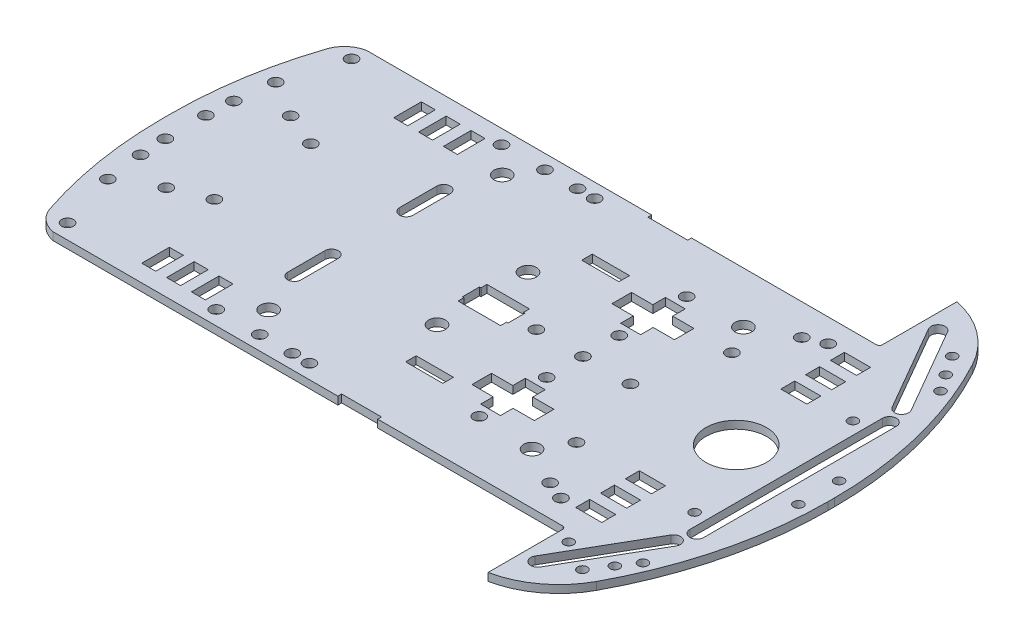
SolidWorks part; units mm, degrees
other "Camera1"
material "Acrylic (Medium-high impact)"
ref_plane "Front Plane" through (0, 0, 0) normal (0, 0, 1) x (1, 0, 0)
ref_plane "Top Plane" through (0, 0, 0) normal (0, 1, 0) x (1, 0, 0)
ref_plane "Right Plane" through (0, 0, 0) normal (1, 0, 0) x (0, 0, -1)
sketch "Sketch1" plane through (0, 0, 0) normal (0, 1, 0) x (1, 0, 0)
  line L0 (165, 101.05) -> (165, 126.05)
  line L1 (0, 0) -> (165, 0)
  line L2 (0, 0) -> (0, 101.05) construction
  line L3 (0, 101.05) -> (165, 101.05)
  line L4 (165, 0) -> (165, 101.05) construction
  line L5 (165, 0) -> (165, -25)
  line L6 (165, 50.525) -> (200, 50.525) construction
  line L7 (200, 49.525) -> (200, 51.525)
  line L8 (185, 111.05) -> (185, -10) construction
  line L9 (185, 111.05) -> (165, 111.05) construction
  line L10 (185, -10) -> (165, -10) construction
  line L11 (0, 50.525) -> (-14, 50.525) construction
  line L12 (-14, 49.025) -> (-14, 52.025)
  line L13 (0, 95.05) -> (-7, 95.05) construction
  arc A0 (200, 51.525) -> (185, 111.05) centre (74.3925, 51.525) ccw
  arc A1 (185, 111.05) -> (165, 126.05) centre (158.8001, 96.9502) ccw
  arc A2 (200, 49.525) -> (185, -10) centre (74.3925, 49.525) cw
  arc A3 (185, -10) -> (165, -25) centre (158.8001, 4.0998) cw
  arc A4 (-14, 52.025) -> (-7, 95.05) centre (121.725, 52.025) cw
  arc A5 (-7, 95.05) -> (0, 101.05) centre (1.5093, 92.2059) cw
  arc A6 (-14, 49.025) -> (-7, 6) centre (121.725, 49.025) ccw
  arc A7 (-7, 6) -> (0, 0) centre (1.5093, 8.8441) ccw
  point P19 (185, 50.525)
  dimension "D1" = 101.05
  dimension "D2" = 165
  dimension "D3" = 25
  dimension "D4" = 35
  dimension "D5" = 2
  dimension "D6" = 20
  dimension "D7" = 15
  dimension "D8" = 14
  dimension "D9" = 3
  dimension "D10" = 7
  dimension "D11" = 6
extrude "Boss-Extrude1" add sketch "Sketch1" along normal blind 2.5
fillet "Fillet1" radius 1 2 edges at (165, 1.25, 0) (165, 1.25, -101.05)
sketch "Sketch2" plane through (0, 2.5, 0) normal (0, 1, 0) x (1, 0, 0)
  line L0 (104.5, 101.05) -> (104.5, 0) construction
  line L1 (164, 101.05) -> (0, 101.05) construction
  line L2 (0, 0) -> (164, 0) construction
  line L3 (165, 126.05) -> (165, 102.05) construction
  line L4 (104.5, 101.05) -> (104.5, 99.83)
  line L5 (104.5, 101.05) -> (91.65, 101.05)
  line L6 (104.5, 99.83) -> (91.65, 99.83)
  line L7 (91.65, 101.05) -> (91.65, 99.83)
  line L8 (104.5, 50.525) -> (200, 50.525) construction
  line L9 (200, 49.525) -> (200, 51.525) construction
  line L10 (104.5, 1.22) -> (91.65, 1.22)
  line L11 (91.65, 0) -> (91.65, 1.22)
  line L12 (104.5, 0) -> (91.65, 0)
  line L13 (104.5, 0) -> (104.5, 1.22)
  dimension "D1" = 60.5
  dimension "D2" = 1.22
  dimension "D3" = 12.85
extrude "Cut-Extrude1" cut sketch "Sketch2" against normal up to surface (2.5 mm away) up to face at (107.6229, 0, -50.525)
sketch "Sketch3" plane through (0, 2.5, 0) normal (0, 1, 0) x (1, 0, 0)
  line L0 (0, 101.05) -> (0, 0) construction
  line L1 (23, 101.05) -> (23, 0) construction
  line L2 (91.65, 101.05) -> (0, 101.05) construction
  line L3 (0, 0) -> (91.65, 0) construction
  line L4 (23, 95.55) -> (23, 86.65)
  line L5 (23, 95.55) -> (27.5, 95.55)
  line L6 (23, 86.65) -> (27.5, 86.65)
  line L7 (27.5, 95.55) -> (27.5, 86.65)
  line L8 (29.25, 101.05) -> (29.25, 0) construction
  line L9 (35.5, 86.65) -> (31, 86.65)
  line L10 (31, 95.55) -> (31, 86.65)
  line L11 (35.5, 95.55) -> (31, 95.55)
  line L12 (35.5, 95.55) -> (35.5, 86.65)
  line L13 (37.25, 101.05) -> (37.25, 0) construction
  line L14 (39, 95.55) -> (39, 86.65)
  line L15 (39, 95.55) -> (43.5, 95.55)
  line L16 (43.5, 95.55) -> (43.5, 86.65)
  line L17 (39, 86.65) -> (43.5, 86.65)
  line L18 (23, 50.525) -> (37.25, 50.525) construction
  line L19 (39, 5.5) -> (43.5, 5.5)
  line L20 (43.5, 5.5) -> (43.5, 14.4)
  line L21 (39, 14.4) -> (43.5, 14.4)
  line L22 (39, 5.5) -> (39, 14.4)
  line L23 (35.5, 5.5) -> (35.5, 14.4)
  line L24 (35.5, 5.5) -> (31, 5.5)
  line L25 (31, 5.5) -> (31, 14.4)
  line L26 (35.5, 14.4) -> (31, 14.4)
  line L27 (23, 14.4) -> (27.5, 14.4)
  line L28 (27.5, 5.5) -> (27.5, 14.4)
  line L29 (23, 5.5) -> (27.5, 5.5)
  line L30 (23, 5.5) -> (23, 14.4)
  dimension "D1" = 23
  dimension "D2" = 5.5
  dimension "D3" = 8.9
  dimension "D4" = 4.5
  dimension "D5" = 1.75
  dimension "D6" = 1.75
extrude "Cut-Extrude2" cut sketch "Sketch3" against normal up to surface (2.5 mm away) up to face at (104.4403, 0, -50.525)
sketch "Sketch4" plane through (0, 2.5, 0) normal (0, 1, 0) x (1, 0, 0)
  line L0 (0, 0) -> (0, 101.05) construction
  line L1 (0, 50.525) -> (84, 50.525) construction
  line L2 (84, 55.175) -> (84, 45.875) construction
  line L3 (84, 55.175) -> (84, 45.875) construction
  line L4 (84, 55.175) -> (98.66, 55.175) construction
  line L5 (84, 45.875) -> (98.66, 45.875) construction
  line L6 (98.66, 55.175) -> (98.66, 45.875) construction
  line L7 (84.48, 55.175) -> (84.48, 45.875) construction
  line L8 (98.18, 55.175) -> (98.18, 45.875) construction
  line L9 (91.33, 55.175) -> (91.33, 45.875) construction
  line L10 (84.48, 55.175) -> (84.48, 53.245)
  line L11 (84.48, 53.245) -> (84, 53.245)
  line L12 (84, 53.245) -> (84, 47.805)
  line L13 (84, 47.805) -> (84.48, 47.805)
  line L14 (84.48, 47.805) -> (84.48, 45.875)
  line L15 (84.48, 45.875) -> (98.18, 45.875)
  line L16 (98.18, 45.875) -> (98.18, 47.805)
  line L17 (98.18, 47.805) -> (98.66, 47.805)
  line L18 (98.66, 47.805) -> (98.66, 53.245)
  line L19 (98.66, 53.245) -> (98.18, 53.245)
  line L20 (98.18, 53.245) -> (98.18, 55.175)
  line L21 (98.18, 55.175) -> (84.48, 55.175)
  point P14 (84.48, 53.245)
  point P17 (98.18, 53.245)
  point P18 (98.18, 47.805)
  point P19 (84.48, 47.805)
  dimension "D1" = 84
  dimension "D2" = 9.3
  dimension "D3" = 14.66
  dimension "D4" = 0.48
  dimension "D5" = 0.48
  dimension "D6" = 2.72
extrude "Cut-Extrude3" cut sketch "Sketch4" against normal up to surface (2.5 mm away) up to face at (25.25, 0, -9.95)
sketch "Sketch5" plane through (0, 2.5, 0) normal (0, 1, 0) x (1, 0, 0)
  line L0 (84, 50.525) -> (160.0831, 50.525) construction
  line L1 (84, 53.245) -> (84, 47.805) construction
  line L2 (116.86, 65.875) -> (120.06, 65.875)
  line L3 (116.86, 69.925) -> (116.86, 65.875)
  line L4 (110.01, 69.925) -> (116.86, 69.925)
  line L5 (98.66, 47.805) -> (98.66, 53.245) construction
  line L6 (120.06, 50.525) -> (120.06, 101.05) construction
  line L7 (164, 101.05) -> (104.5, 101.05) construction
  line L8 (130.11, 73.075) -> (120.06, 73.075) construction
  line L9 (120.06, 80.275) -> (123.26, 80.275) construction
  line L10 (116.86, 80.275) -> (123.26, 80.275)
  line L11 (123.26, 80.275) -> (123.26, 76.225)
  line L12 (123.26, 76.225) -> (130.11, 76.225)
  line L13 (130.11, 76.225) -> (130.11, 69.925)
  line L14 (130.11, 69.925) -> (123.26, 69.925)
  line L15 (123.26, 69.925) -> (123.26, 65.875)
  line L16 (123.26, 65.875) -> (120.06, 65.875)
  line L17 (110.01, 76.225) -> (110.01, 69.925)
  line L18 (116.86, 76.225) -> (110.01, 76.225)
  line L19 (116.86, 80.275) -> (116.86, 76.225)
  line L20 (116.86, 31.125) -> (116.86, 35.175)
  line L21 (110.01, 31.125) -> (116.86, 31.125)
  line L22 (110.01, 24.825) -> (110.01, 31.125)
  line L23 (116.86, 24.825) -> (110.01, 24.825)
  line L24 (116.86, 20.775) -> (116.86, 24.825)
  line L25 (116.86, 20.775) -> (123.26, 20.775)
  line L26 (123.26, 20.775) -> (123.26, 24.825)
  line L27 (123.26, 24.825) -> (130.11, 24.825)
  line L28 (130.11, 24.825) -> (130.11, 31.125)
  line L29 (130.11, 31.125) -> (123.26, 31.125)
  line L30 (123.26, 31.125) -> (123.26, 35.175)
  line L31 (123.26, 35.175) -> (120.06, 35.175)
  line L32 (116.86, 35.175) -> (120.06, 35.175)
  circle A0 centre (105.06, 50.525) radius 1.9
  circle A1 centre (120.06, 50.525) radius 1.9
  circle A2 centre (135.36, 50.525) radius 1.9
  circle A3 centre (120.06, 62.225) radius 1.9
  circle A4 centre (120.06, 83.925) radius 1.9
  circle A5 centre (120.06, 17.125) radius 1.9
  circle A6 centre (120.06, 38.825) radius 1.9
  point P6 (106.96, 50.525)
  point P7 (103.16, 50.525)
  point P8 (133.46, 50.525)
  point P12 (121.96, 50.525)
  point P13 (121.96, 50.525)
  point P14 (118.16, 50.525)
  point P23 (120.06, 60.325)
  point P24 (120.06, 52.425)
  point P27 (120.06, 82.025)
  point P29 (121.66, 65.875)
  point P32 (120.06, 64.125)
  dimension "D5" = 3.8
  dimension "D1" = 3.8
  dimension "D4" = 3.8
  dimension "D7" = 3.8
  dimension "D9" = 3.8
  dimension "D2" = 4.5
  dimension "D3" = 19.5
  dimension "D6" = 34.8
  dimension "D8" = 7.9
  dimension "D10" = 14.4
  dimension "D11" = 1.75
  dimension "D12" = 1.75
  dimension "D13" = 3.2
  dimension "D14" = 10.05
  dimension "D15" = 6.3
extrude "Cut-Extrude4" cut sketch "Sketch5" against normal up to surface (2.5 mm away) up to face at (91.33, 0, -50.525)
sketch "Sketch6" plane through (0, 2.5, 0) normal (0, 1, 0) x (1, 0, 0)
  line L0 (0, 101.05) -> (0, 0) construction
  line L1 (93, 101.05) -> (93, 0) construction
  line L2 (91.65, 101.05) -> (0, 101.05) construction
  line L3 (0, 0) -> (91.65, 0) construction
  line L4 (105, 101.05) -> (105, 0) construction
  line L5 (105, 80.58) -> (93, 80.58) construction
  line L7 (91.65, 99.83) -> (104.5, 99.83) construction
  line L9 (93, 80.58) -> (105, 80.58)
  line L10 (93, 77.18) -> (105, 77.18)
  line L11 (105, 77.18) -> (105, 80.58)
  line L12 (93, 80.58) -> (93, 77.18)
  line L13 (0, 50.525) -> (200, 50.525) construction
  line L14 (200, 49.525) -> (200, 51.525) construction
  line L15 (93, 20.47) -> (105, 20.47)
  line L16 (105, 23.87) -> (105, 20.47)
  line L17 (93, 23.87) -> (105, 23.87)
  line L18 (93, 20.47) -> (93, 23.87)
  dimension "D1" = 93
  dimension "D2" = 105
  dimension "D3" = 19.25
  dimension "D4" = 3.4
extrude "Cut-Extrude5" cut sketch "Sketch6" against normal up to surface (2.5 mm away) up to face at (105.06, 0, -48.625)
sketch "Sketch7" plane through (0, 2.5, 0) normal (0, 1, 0) x (1, 0, 0)
  line L0 (0, 101.05) -> (0, 0) construction
  line L1 (161, 101.05) -> (161, 0) construction
  line L2 (164, 101.05) -> (104.5, 101.05) construction
  line L3 (104.5, 0) -> (164, 0) construction
  line L4 (169.4, 124.7509) -> (169.4, -23.7009) construction
  line L5 (161, 93.8) -> (169.4, 93.8)
  line L6 (161, 93.8) -> (161, 89.3)
  line L7 (169.4, 93.8) -> (169.4, 89.3)
  line L8 (161, 89.3) -> (169.4, 89.3)
  line L11 (161, 85.8) -> (169.4, 85.8)
  line L12 (161, 85.8) -> (161, 81.3)
  line L13 (169.4, 85.8) -> (169.4, 81.3)
  line L14 (161, 81.3) -> (169.4, 81.3)
  line L15 (161, 77.8) -> (169.4, 77.8)
  line L16 (161, 77.8) -> (161, 73.3)
  line L17 (169.4, 77.8) -> (169.4, 73.3)
  line L18 (161, 73.3) -> (169.4, 73.3)
  line L19 (0, 50.525) -> (169.4, 50.525) construction
  line L20 (169.4, 23.25) -> (169.4, 27.75)
  line L21 (161, 27.75) -> (169.4, 27.75)
  line L22 (161, 23.25) -> (161, 27.75)
  line L23 (161, 23.25) -> (169.4, 23.25)
  line L24 (169.4, 15.25) -> (169.4, 19.75)
  line L25 (161, 19.75) -> (169.4, 19.75)
  line L26 (161, 15.25) -> (161, 19.75)
  line L27 (161, 15.25) -> (169.4, 15.25)
  line L28 (169.4, 7.25) -> (169.4, 11.75)
  line L29 (161, 11.75) -> (169.4, 11.75)
  line L30 (161, 7.25) -> (161, 11.75)
  line L31 (161, 7.25) -> (169.4, 7.25)
  arc A0 (185, 111.05) -> (165, 126.05) centre (158.8001, 96.9502) ccw construction
  arc A1 (165, -25) -> (185, -10) centre (158.8001, 4.0998) ccw construction
  dimension "D1" = 161
  dimension "D2" = 8.4
  dimension "D3" = 7.25
  dimension "D4" = 4.5
  dimension "D5" = 4.5
  dimension "D6" = 4.5
  dimension "D7" = 3.5
  dimension "D8" = 3.5
extrude "Cut-Extrude6" cut sketch "Sketch7" against normal up to surface (2.5 mm away) up to face at (99, 0, -78.88)
sketch "Sketch8" plane through (0, 2.5, 0) normal (0, 1, 0) x (1, 0, 0)
  line L0 (98.66, 50.525) -> (169.41, 50.525) construction
  line L1 (98.66, 47.805) -> (98.66, 53.245) construction
  circle A0 centre (169.41, 50.525) radius 9.75
  dimension "D2" = 19.5
  dimension "D1" = 70.75
extrude "Cut-Extrude7" cut sketch "Sketch8" against normal up to surface (2.5 mm away) up to face at (165.2, 0, -91.55)
sketch "Sketch9" plane through (0, 2.5, 0) normal (0, 1, 0) x (1, 0, 0)
  line L0 (0, 101.05) -> (0, 0) construction
  line L1 (87.7, 55.175) -> (87.7, 101.05) construction
  line L2 (98.18, 55.175) -> (84.48, 55.175) construction
  line L3 (91.65, 101.05) -> (0, 101.05) construction
  line L4 (98.66, 50.525) -> (0, 50.525) construction
  line L5 (98.66, 47.805) -> (98.66, 53.245) construction
  line L6 (56.45, 101.05) -> (56.45, 0) construction
  line L7 (0, 0) -> (91.65, 0) construction
  circle A0 centre (87.7, 65.175) radius 2.7
  circle A1 centre (87.7, 35.875) radius 2.7
  circle A2 centre (56.45, 88.15) radius 2.7
  circle A3 centre (56.45, 12.9) radius 2.7
  dimension "D3" = 5.4
  dimension "D6" = 5.4
  dimension "D1" = 87.7
  dimension "D2" = 10
  dimension "D4" = 56.45
  dimension "D5" = 12.9
extrude "Cut-Extrude8" cut sketch "Sketch9" against normal up to surface (2.5 mm away) up to face at (169.41, 0, -40.775)
sketch "Sketch10" plane through (0, 2.5, 0) normal (0, 1, 0) x (1, 0, 0)
  line L0 (0, 101.05) -> (0, 0) construction
  line L1 (47.9, 101.05) -> (47.9, 0) construction
  line L2 (91.65, 101.05) -> (0, 101.05) construction
  line L3 (0, 0) -> (91.65, 0) construction
  line L4 (61.9, 101.05) -> (61.9, 0) construction
  line L5 (72.4, 101.05) -> (72.4, 0) construction
  line L6 (77.9, 101.05) -> (77.9, 0) construction
  line L7 (47.9, 96.45) -> (77.9, 96.45) construction
  line L8 (0, 50.525) -> (179.16, 50.525) construction
  circle A1 centre (47.9, 96.45) radius 1.9
  circle A2 centre (61.9, 96.45) radius 1.9
  circle A3 centre (72.4, 96.45) radius 1.9
  circle A4 centre (77.9, 96.45) radius 1.9
  circle A5 centre (169.41, 50.525) radius 9.75 construction
  circle A6 centre (77.9, 4.6) radius 1.9
  circle A7 centre (72.4, 4.6) radius 1.9
  circle A8 centre (61.9, 4.6) radius 1.9
  circle A9 centre (47.9, 4.6) radius 1.9
  dimension "D1" = 47.9
  dimension "D6" = 3.8
  dimension "D7" = 3.8
  dimension "D8" = 3.8
  dimension "D9" = 3.8
  dimension "D2" = 61.9
  dimension "D3" = 72.4
  dimension "D4" = 77.9
  dimension "D5" = 4.6
extrude "Cut-Extrude9" cut sketch "Sketch10" against normal up to surface (2.5 mm away) up to face at (56.45, 0, -10.2)
sketch "Sketch11" plane through (0, 2.5, 0) normal (0, 1, 0) x (1, 0, 0)
  line L0 (0, 101.05) -> (0, 0) construction
  line L1 (91.65, 101.05) -> (0, 101.05) construction
  line L2 (98.66, 50.525) -> (0, 50.525) construction
  line L3 (98.66, 47.805) -> (98.66, 53.245) construction
  circle A0 centre (-0.2, 96.25) radius 1.9
  circle A1 centre (-0.2, 4.8) radius 1.9
  circle A2 centre (-5.9, 77.55) radius 1.9
  circle A3 centre (-7.4, 65.55) radius 1.9
  circle A4 centre (-7.9, 57.05) radius 1.9
  circle A5 centre (-7.9, 44) radius 1.9
  circle A6 centre (-7.4, 35.5) radius 1.9
  circle A7 centre (-5.9, 23.5) radius 1.9
  dimension "D2" = 3.8
  dimension "D5" = 3.8
  dimension "D7" = 3.8
  dimension "D11" = 3.8
  dimension "D1" = 0.2
  dimension "D3" = 4.8
  dimension "D4" = 5.9
  dimension "D6" = 23.5
  dimension "D8" = 35.5
  dimension "D9" = 7.4
  dimension "D10" = 44
  dimension "D12" = 7.9
extrude "Cut-Extrude10" cut sketch "Sketch11" against normal up to surface (2.5 mm away) up to face at (61.9, 0, -94.55)
sketch "Sketch12" plane through (0, 2.5, 0) normal (0, 1, 0) x (1, 0, 0)
  line L0 (0, 101.05) -> (0, 0) construction
  line L1 (91.65, 101.05) -> (0, 101.05) construction
  line L2 (0, 50.525) -> (98.66, 50.525) construction
  line L3 (98.66, 47.805) -> (98.66, 53.245) construction
  circle A0 centre (5.9, 70.55) radius 1.9
  circle A1 centre (16.9, 66.05) radius 1.9
  circle A2 centre (5.9, 30.5) radius 1.9
  circle A3 centre (16.9, 35) radius 1.9
  dimension "D1" = 3.8
  dimension "D4" = 3.8
  dimension "D2" = 5.9
  dimension "D3" = 30.5
  dimension "D5" = 35
  dimension "D6" = 16.9
extrude "Cut-Extrude11" cut sketch "Sketch12" against normal up to surface (2.5 mm away) up to face at (-0.2, 0, -94.35)
sketch "Sketch13" plane through (0, 2.5, 0) normal (0, 1, 0) x (1, 0, 0)
  line L0 (0, 101.05) -> (0, 0) construction
  line L1 (0, 50.525) -> (200, 50.525) construction
  line L2 (200, 49.525) -> (200, 51.525) construction
  circle A0 centre (196, 57.075) radius 1.55
  circle A1 centre (196, 43.975) radius 1.55
  circle A2 centre (181.5, 25.025) radius 1.55
  circle A3 centre (181.5, 76.025) radius 1.55
  dimension "D1" = 3.1
  dimension "D5" = 3.1
  dimension "D2" = 6.55
  dimension "D3" = 196
  dimension "D4" = 181.5
  dimension "D6" = 25.5
extrude "Cut-Extrude12" cut sketch "Sketch13" against normal up to surface (2.5 mm away) up to face at (5.9, 0, -68.65)
sketch "Sketch14" plane through (0, 2.5, 0) normal (0, 1, 0) x (1, 0, 0)
  line L0 (165, -1) -> (165, -25) construction
  line L1 (104.5, 0) -> (164, 0) construction
  line L2 (98.66, 50.525) -> (179.16, 50.525) construction
  line L3 (98.66, 47.805) -> (98.66, 53.245) construction
  circle A0 centre (169.5, -3.5) radius 1.55
  circle A1 centre (169.41, 50.525) radius 9.75 construction
  dimension "D1" = 3.1
  dimension "D2" = 4.5
  dimension "D3" = 3.5
extrude "Cut-Extrude13" cut sketch "Sketch14" against normal up to surface (2.5 mm away) up to face at (181.5, 0, -74.475)
sketch "Sketch15" plane through (0, 2.5, 0) normal (0, 1, 0) x (1, 0, 0)
  line L0 (0, 0) -> (0, 101.05) construction
  line L1 (104.5, 0) -> (164, 0) construction
  line L2 (0, 50.525) -> (179.16, 50.525) construction
  circle A0 centre (137.7, 16.5) radius 2.7
  circle A1 centre (169.41, 50.525) radius 9.75 construction
  circle A2 centre (137.7, 84.55) radius 2.7
  dimension "D1" = 5.4
  dimension "D2" = 137.7
  dimension "D3" = 16.5
extrude "Cut-Extrude14" cut sketch "Sketch15" against normal up to surface (2.5 mm away) up to face at (169.5, 0, 5.05)
sketch "Sketch16" plane through (0, 2.5, 0) normal (0, 1, 0) x (1, 0, 0)
  line L0 (0, 0) -> (0, 101.05) construction
  line L1 (104.5, 0) -> (164, 0) construction
  line L2 (0, 50.525) -> (159.66, 50.525) construction
  circle A0 centre (143, 25.5) radius 1.9
  circle A1 centre (169.41, 50.525) radius 9.75 construction
  circle A2 centre (143, 75.55) radius 1.9
  dimension "D1" = 3.8
  dimension "D2" = 143
  dimension "D3" = 25.5
extrude "Cut-Extrude15" cut sketch "Sketch16" against normal up to surface (2.5 mm away) up to face at (137.7, 0, -13.8)
sketch "Sketch17" plane through (0, 2.5, 0) normal (0, 1, 0) x (1, 0, 0)
  line L0 (0, 0) -> (0, 101.05) construction
  line L1 (104.5, 0) -> (164, 0) construction
  line L2 (0, 50.525) -> (179.16, 50.525) construction
  circle A0 centre (150, 10) radius 1.9
  circle A1 centre (156, 7.5) radius 1.9
  circle A2 centre (169.41, 50.525) radius 9.75 construction
  circle A3 centre (150, 91.05) radius 1.9
  circle A4 centre (156, 93.55) radius 1.9
  dimension "D1" = 3.8
  dimension "D4" = 3.8
  dimension "D2" = 150
  dimension "D3" = 10
  dimension "D5" = 156
  dimension "D6" = 7.5
extrude "Cut-Extrude16" cut sketch "Sketch17" against normal up to surface (2.5 mm away) up to face at (143, 0, -23.6)
sketch "Sketch18" plane through (0, 2.5, 0) normal (0, 1, 0) x (1, 0, 0)
  line L0 (49, 101.05) -> (49, 0) construction
  line L1 (91.65, 101.05) -> (0, 101.05) construction
  line L2 (0, 0) -> (91.65, 0) construction
  line L3 (0, 101.05) -> (0, 0) construction
  line L4 (53.3, 101.05) -> (53.3, 0) construction
  line L5 (49, 74.55) -> (53.3, 74.55) construction
  line L6 (49, 62.55) -> (53.3, 62.55) construction
  line L7 (49, 74.55) -> (49, 62.55)
  line L8 (53.3, 74.55) -> (53.3, 62.55)
  line L9 (0, 50.525) -> (53.3, 50.525) construction
  line L10 (53.3, 26.5) -> (53.3, 38.5)
  line L11 (49, 26.5) -> (49, 38.5)
  arc A0 (49, 74.55) -> (53.3, 74.55) centre (51.15, 74.55) cw
  arc A1 (53.3, 62.55) -> (49, 62.55) centre (51.15, 62.55) cw
  arc A2 (49, 26.5) -> (53.3, 26.5) centre (51.15, 26.5) ccw
  arc A3 (53.3, 38.5) -> (49, 38.5) centre (51.15, 38.5) ccw
  dimension "D1" = 4.3
  dimension "D2" = 49
  dimension "D3" = 26.5
  dimension "D4" = 12
extrude "Cut-Extrude17" cut sketch "Sketch18" against normal up to surface (2.5 mm away) up to face at (156, 0, -5.6)
sketch "Sketch19" plane through (0, 2.5, 0) normal (0, 1, 0) x (1, 0, 0)
  line L0 (185.5, 101.05) -> (185.5, 0) construction
  line L1 (164, 101.05) -> (104.5, 101.05) construction
  line L2 (104.5, 0) -> (164, 0) construction
  line L3 (0, 0) -> (0, 101.05) construction
  line L4 (190, 101.05) -> (190, 0) construction
  line L5 (190, 50.525) -> (0, 50.525) construction
  line L6 (190, 19.525) -> (190, 81.525)
  line L7 (190, 81.525) -> (185.5, 81.525) construction
  line L8 (185.5, 81.525) -> (185.5, 19.525)
  arc A0 (190, 81.525) -> (185.5, 81.525) centre (187.75, 81.525) ccw
  arc A1 (190, 19.525) -> (185.5, 19.525) centre (187.75, 19.525) cw
  point P20 (185.5, 50.525)
  dimension "D1" = 185.5
  dimension "D2" = 4.5
  dimension "D3" = 31
extrude "Cut-Extrude18" cut sketch "Sketch19" against normal up to surface (2.5 mm away) up to face at (51.15, 0, -68.55)
sketch "Sketch20" plane through (0, 2.5, 0) normal (0, 1, 0) x (1, 0, 0)
  line L0 (165, -18) -> (184, 14.909) construction
  line L1 (165, -1) -> (165, -25) construction
  line L2 (187.8971, 12.659) -> (165, -27) construction
  line L3 (187.8971, 12.659) -> (184, 14.909) construction
  line L4 (168, -12.8038) -> (171.8971, -15.0538) construction
  line L5 (168, -12.8038) -> (184, 14.909)
  line L6 (187.8971, 12.659) -> (171.8971, -15.0538)
  line L7 (0, 0) -> (0, 101.05) construction
  line L8 (0, 50.525) -> (190, 50.525) construction
  line L9 (190, 19.525) -> (190, 81.525) construction
  line L10 (168, 113.8538) -> (184, 86.141)
  line L11 (187.8971, 88.391) -> (171.8971, 116.1038)
  arc A0 (184, 14.909) -> (187.8971, 12.659) centre (185.9486, 13.784) cw
  arc A1 (168, -12.8038) -> (171.8971, -15.0538) centre (169.9486, -13.9288) ccw
  arc A2 (184, 86.141) -> (187.8971, 88.391) centre (185.9486, 87.266) ccw
  arc A3 (168, 113.8538) -> (171.8971, 116.1038) centre (169.9486, 114.9788) cw
  point P9 (185.9486, 13.784)
  dimension "D1" = 30
  dimension "D2" = 7
  dimension "D3" = 0
  dimension "D4" = 4.5
  dimension "D5" = 6
  dimension "D6" = 32
extrude "Cut-Extrude19" cut sketch "Sketch20" against normal up to surface (2.5 mm away) up to face at (187.75, 0, -50.525)
sketch "Sketch21" plane through (0, 2.5, 0) normal (0, 1, 0) x (1, 0, 0)
  line L0 (183.3971, 4.8647) -> (187.2942, 2.6147) construction
  line L1 (171.8971, -15.0538) -> (187.8971, 12.659) construction
  line L2 (179.4282, -9.0096) -> (176.3971, -7.2596) construction
  line L3 (180.1471, -0.7644) -> (183.6112, -2.7644) construction
  line L4 (190, 50.525) -> (84, 50.525) construction
  line L5 (190, 19.525) -> (190, 81.525) construction
  line L6 (84, 53.245) -> (84, 47.805) construction
  circle A0 centre (187.2942, 2.6147) radius 1.55
  circle A2 centre (179.4282, -9.0096) radius 1.55
  circle A3 centre (183.6112, -2.7644) radius 1.55
  circle A5 centre (179.4282, 110.0596) radius 1.55
  circle A6 centre (183.6112, 103.8144) radius 1.55
  circle A7 centre (187.2942, 98.4353) radius 1.55
  dimension "D5" = 3.1
  dimension "D6" = 90
  dimension "D10" = 3.1
  dimension "D12" = 3.1
  dimension "D1" = 4.5
  dimension "D2" = 9
  dimension "D3" = 3.5
  dimension "D4" = 90
  dimension "D7" = 23
  dimension "D8" = 90
  dimension "D9" = 4
  dimension "D11" = 15.5
extrude "Cut-Extrude20" cut sketch "Sketch21" against normal up to surface (2.5 mm away) up to face at (177.9486, 0, 0.0724)
